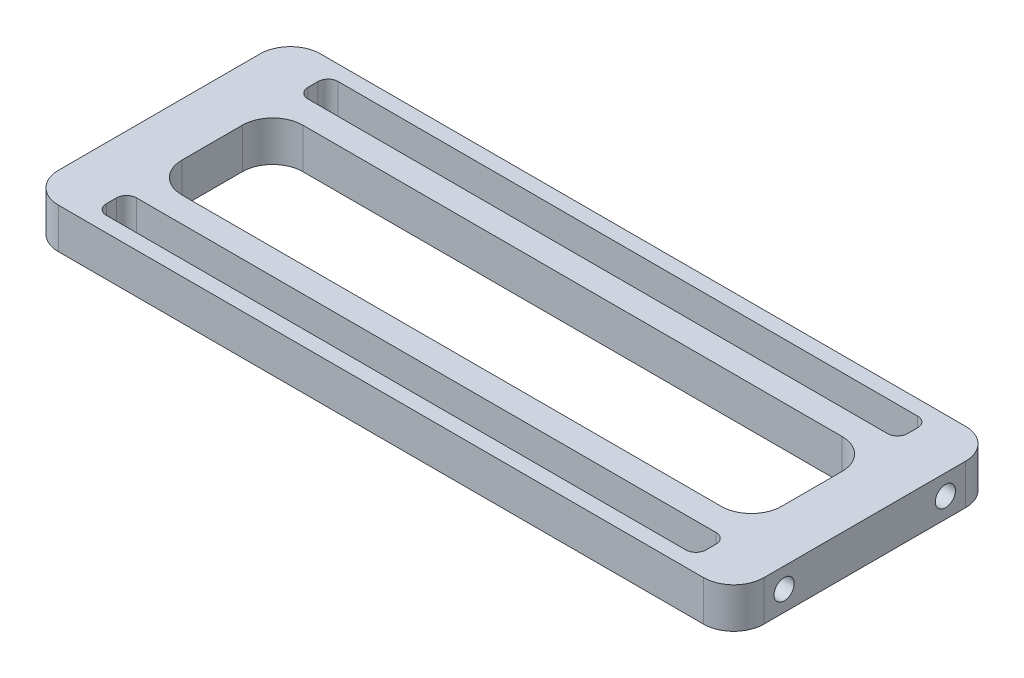
SolidWorks part; units mm, degrees
material "1060 Alloy"
ref_plane "Front Plane" through (0, 0, 0) normal (0, 0, 1) x (1, 0, 0)
ref_plane "Top Plane" through (0, 0, 0) normal (0, 1, 0) x (1, 0, 0)
ref_plane "Right Plane" through (0, 0, 0) normal (1, 0, 0) x (0, 0, -1)
sketch "Sketch1" plane through (0, 0, 0) normal (0, 1, 0) x (1, 0, 0)
  line L1 (-32, -13) -> (32, -13)
  line L2 (-35, -10) -> (-35, 10)
  line L3 (-32, 13) -> (32, 13)
  line L4 (35, -10) -> (35, 10)
  line L5 (-35, -13) -> (35, 13) construction
  line L6 (-35, 13) -> (35, -13) construction
  line L7 (-26.7498, -6) -> (26.7498, -6)
  line L8 (-29.7498, -3) -> (-29.7498, 3)
  line L9 (-26.7498, 6) -> (26.7498, 6)
  line L10 (29.7498, -3) -> (29.7498, 3)
  line L11 (-29.7498, -6) -> (29.7498, 6) construction
  line L12 (-29.7498, 6) -> (29.7498, -6) construction
  line L13 (-28.7498, 11.5) -> (28.7498, 11.5)
  line L14 (-29.7498, 10.5) -> (-29.7498, 9.5)
  line L15 (-28.7498, 8.5) -> (28.7498, 8.5)
  line L16 (29.7498, 10.5) -> (29.7498, 9.5)
  line L17 (-29.7498, 11.5) -> (29.7498, 8.5) construction
  line L18 (-29.7498, 8.5) -> (29.7498, 11.5) construction
  line L19 (-29.7498, -10.5) -> (-29.7498, -9.5)
  line L20 (-28.7498, -11.5) -> (28.7498, -11.5)
  line L21 (29.7498, -10.5) -> (29.7498, -9.5)
  line L22 (-28.7498, -8.5) -> (28.7498, -8.5)
  arc A0 (35, 10) -> (32, 13) centre (32, 10) ccw
  arc A1 (35, -10) -> (32, -13) centre (32, -10) cw
  arc A2 (-32, -13) -> (-35, -10) centre (-32, -10) cw
  arc A3 (-35, 10) -> (-32, 13) centre (-32, 10) cw
  arc A4 (29.7498, 3) -> (26.7498, 6) centre (26.7498, 3) ccw
  arc A5 (29.7498, -3) -> (26.7498, -6) centre (26.7498, -3) cw
  arc A6 (-26.7498, -6) -> (-29.7498, -3) centre (-26.7498, -3) cw
  arc A7 (-26.7498, 6) -> (-29.7498, 3) centre (-26.7498, 3) ccw
  arc A8 (-29.7498, -10.5) -> (-28.7498, -11.5) centre (-28.7498, -10.5) ccw
  arc A9 (-29.7498, -9.5) -> (-28.7498, -8.5) centre (-28.7498, -9.5) cw
  arc A10 (28.7498, -11.5) -> (29.7498, -10.5) centre (28.7498, -10.5) ccw
  arc A11 (29.7498, -9.5) -> (28.7498, -8.5) centre (28.7498, -9.5) ccw
  arc A12 (29.7498, 9.5) -> (28.7498, 8.5) centre (28.7498, 9.5) cw
  arc A13 (29.7498, 10.5) -> (28.7498, 11.5) centre (28.7498, 10.5) ccw
  arc A14 (-29.7498, 9.5) -> (-28.7498, 8.5) centre (-28.7498, 9.5) ccw
  arc A15 (-29.7498, 10.5) -> (-28.7498, 11.5) centre (-28.7498, 10.5) cw
  point P0 (0, 0)
  point P6 (0, 0)
  point P35 (0, 10)
  dimension "D1" = 3
  dimension "D3" = 1
  dimension "D2" = 2.5
extrude "Boss-Extrude1" add sketch "Sketch1" along normal blind 4
sketch "Sketch2" plane through (35, 0, 0) normal (1, 0, 0) x (0, 0, -1)
  line L0 (-10, 0) -> (10, 0) construction
  circle A0 centre (-8, 2) radius 1
  circle A1 centre (8, 2) radius 1
  dimension "D2" = 16
  dimension "D1" = 8
extrude "Cut-Extrude1" cut sketch "Sketch2" against normal blind 5
